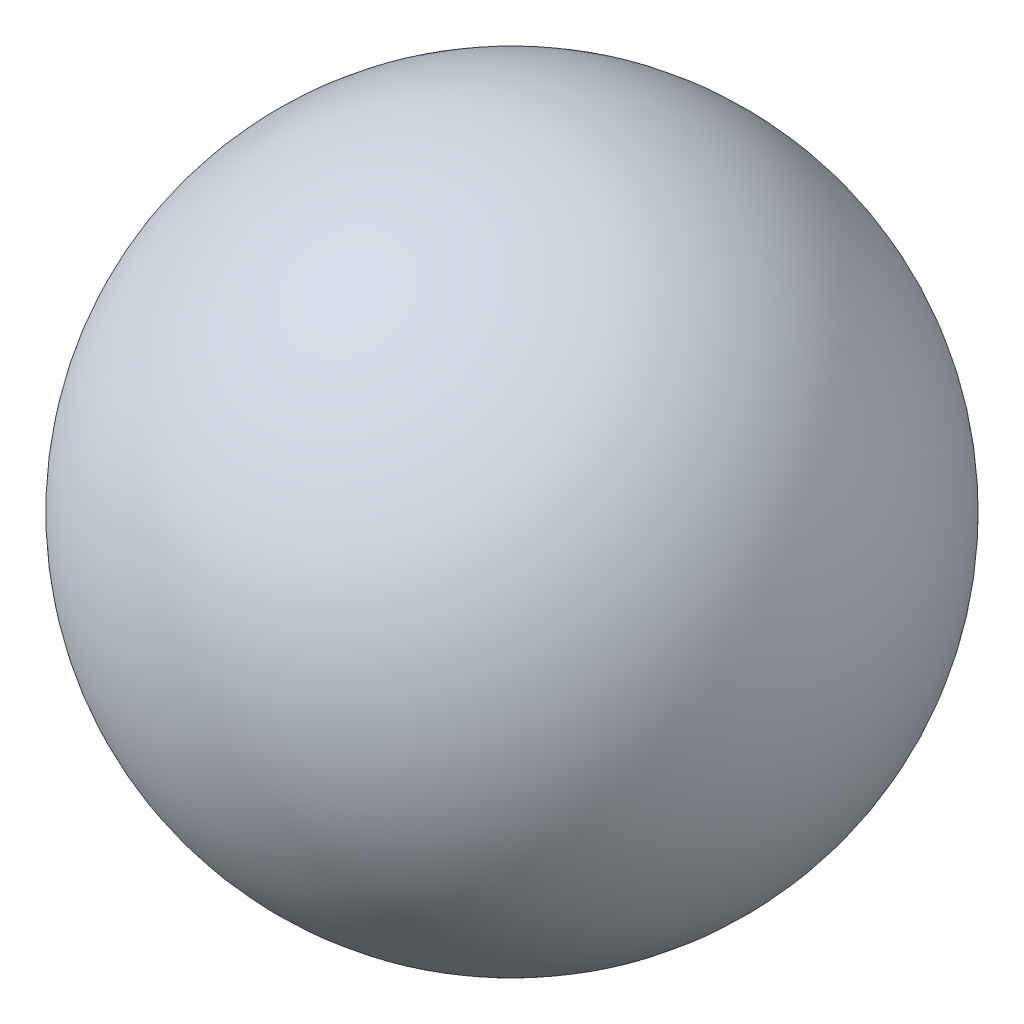
SolidWorks part; units mm, degrees
ref_plane "Front Plane" through (0, 0, 0) normal (0, 0, 1) x (1, 0, 0)
ref_plane "Top Plane" through (0, 0, 0) normal (0, 1, 0) x (1, 0, 0)
ref_plane "Right Plane" through (0, 0, 0) normal (1, 0, 0) x (0, 0, -1)
sketch "Sketch2" plane through (0, 0, 0) normal (1, 0, 0) x (0, 0, -1)
  line L0 (0, 247.65) -> (0, 0)
  arc A0 (0, 0) -> (0, 247.65) centre (0, 123.825) ccw
  point P4 (0, 123.825)
  dimension "D1" = 123.825
revolve "Revolve1" add sketch "Sketch2" angle 360 about L0
sketch "Sketch3" plane through (0, 0, 0) normal (0, 0, 1) x (1, 0, 0)
  point P0 (0, 0)
